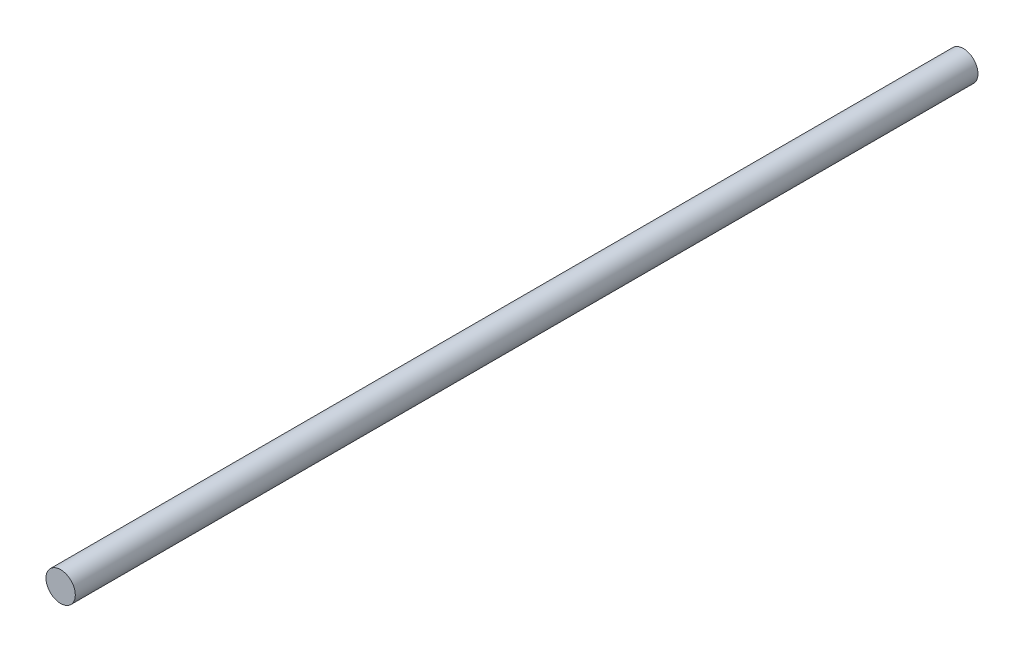
SolidWorks part; units mm, degrees
ref_plane "Front Plane" through (0, 0, 0) normal (0, 0, 1) x (1, 0, 0)
ref_plane "Top Plane" through (0, 0, 0) normal (0, 1, 0) x (1, 0, 0)
ref_plane "Right Plane" through (0, 0, 0) normal (1, 0, 0) x (0, 0, -1)
sketch "Sketch1" plane through (0, 0, 0) normal (0, 0, 1) x (1, 0, 0)
  circle A0 centre (0, 0) radius 0.8255
extrude "Boss-Extrude1" add sketch "Sketch1" along normal blind 50.8
